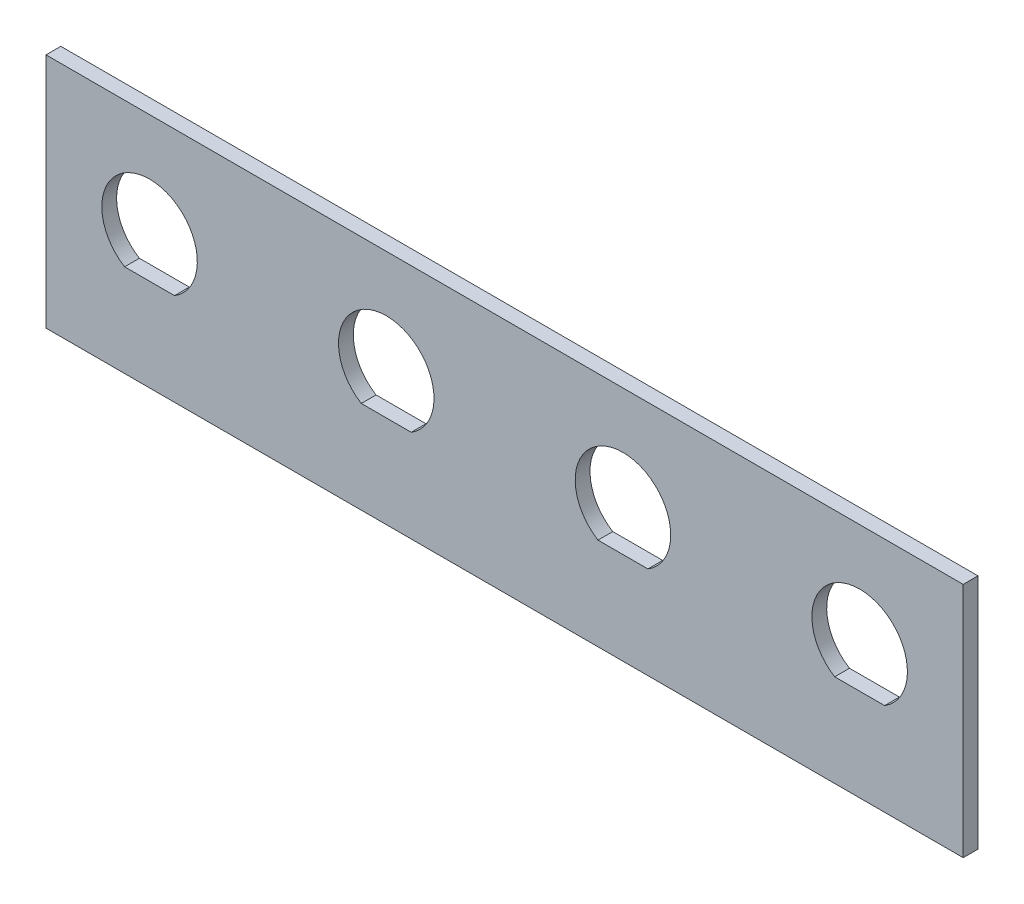
SolidWorks part; units mm, degrees
material "6061-T6 (SS)"
ref_plane "Front Plane" through (0, 0, 0) normal (0, 0, 1) x (1, 0, 0)
ref_plane "Top Plane" through (0, 0, 0) normal (0, 1, 0) x (1, 0, 0)
ref_plane "Right Plane" through (0, 0, 0) normal (1, 0, 0) x (0, 0, -1)
sketch "Sketch1" plane through (0, 0, 0) normal (0, 1, 0) x (1, 0, 0)
  line L1 (101.6, -63.5) -> (-101.6, -63.5)
  line L2 (101.6, -63.5) -> (101.6, 63.5)
  line L3 (101.6, 63.5) -> (-101.6, 63.5)
  line L4 (-101.6, -63.5) -> (-101.6, 63.5)
  line L5 (101.6, -63.5) -> (-101.6, 63.5) construction
  line L6 (101.6, 63.5) -> (-101.6, -63.5) construction
  point P0 (0, 0)
  dimension "D1" = 127
  dimension "D2" = 203.2
extrude "Boss-Extrude1" add sketch "Sketch1" along normal blind 50.8
sketch "Sketch2" plane through (0, 50.8, 0) normal (0, 1, 0) x (1, 0, 0)
  line L8 (-98.425, 60.325) -> (-98.425, -60.325)
  line L9 (98.425, 60.325) -> (-98.425, 60.325)
  line L10 (98.425, -60.325) -> (98.425, 60.325)
  line L11 (-98.425, -60.325) -> (98.425, -60.325)
  line L12 (-98.425, 60.325) -> (-98.425, -60.325)
  line L13 (98.425, 60.325) -> (-98.425, 60.325)
  line L14 (98.425, -60.325) -> (98.425, 60.325)
  line L15 (-98.425, -60.325) -> (98.425, -60.325)
  dimension "D1" = 3.175
extrude "Cut-Extrude1" cut sketch "Sketch2" against normal through all
sketch "Sketch4" plane through (0, 50.8, 0) normal (0, 1, 0) x (1, 0, 0)
  line L4 (101.6, 63.5) -> (-101.6, 63.5)
  line L5 (-101.6, 63.5) -> (-101.6, -63.5)
  line L6 (-101.6, -63.5) -> (101.6, -63.5)
  line L7 (101.6, -63.5) -> (101.6, 63.5)
  line L9 (-98.425, -60.325) -> (98.425, -60.325)
  line L10 (-98.425, -60.325) -> (-98.425, 60.325)
  line L11 (-98.425, 60.325) -> (98.425, 60.325)
  line L12 (98.425, -60.325) -> (98.425, 60.325)
  line L13 (-98.425, -60.325) -> (98.425, 60.325) construction
  line L14 (-98.425, 60.325) -> (98.425, -60.325) construction
  point P12 (0, 0)
  dimension "D1" = 3.175
  dimension "D2" = 3.175
  dimension "D3" = 3.175
  dimension "D4" = 3.175
extrude "Boss-Extrude2" add sketch "Sketch4" against normal blind 6.35
sketch "Sketch10" plane through (0, 0, 63.5) normal (0, 0, 1) x (1, 0, 0)
  line L0 (0, 28.575) -> (50.8, 28.575) construction
  line L1 (-101.6, 0) -> (101.6, 0) construction
  line L3 (-104.775, 19.8374) -> (104.775, 19.8374)
  line L6 (50.8, 28.575) -> (101.6, 28.575) construction
  line L7 (101.6, 50.8) -> (101.6, 0) construction
  line L8 (0, 28.575) -> (-50.8, 28.575) construction
  line L9 (-50.8, 28.575) -> (-101.6, 28.575) construction
  line L10 (-101.6, 50.8) -> (-101.6, 0) construction
  circle A0 centre (-76.2, 28.575) radius 10.2489
  circle A1 centre (-25.4, 28.575) radius 10.2489
  circle A2 centre (25.4, 28.575) radius 10.2489
  circle A3 centre (76.2, 28.575) radius 10.2489
  point P5 (-76.2, 28.575)
  point P9 (-25.4, 28.575)
  point P12 (25.4, 28.575)
  point P13 (76.2, 28.575)
  dimension "D2" = 28.575
  dimension "D1" = 20.4978
  dimension "D3" = 8.7376
extrude "Cut-Extrude5" cut sketch "Sketch10" against normal through all
sketch "Sketch12" plane through (101.6, 0, 0) normal (1, 0, 0) x (0, 0, -1)
  line L0 (63.5, 28.575) -> (-63.5, 28.575) construction
  line L1 (63.5, 50.8) -> (63.5, 0) construction
  line L2 (-63.5, 50.8) -> (-63.5, 0) construction
  line L4 (-63.5, 19.8374) -> (63.5, 19.8374)
  circle A0 centre (-25.4, 28.575) radius 10.2489
  circle A1 centre (25.4, 28.575) radius 10.2489
  point P6 (63.5, 28.575)
  point P7 (-25.4, 28.575)
  point P10 (25.4, 28.575)
  dimension "D2" = 8.7376
  dimension "D3" = 20.4978
  dimension "D1" = 38.1
  dimension "D4" = 38.1
extrude "Cut-Extrude6" cut sketch "Sketch12" against normal up to next
sketch "Sketch13" plane through (-101.6, 0, 0) normal (-1, 0, 0) x (0, 0, 1)
  line L0 (63.5, 25.4) -> (-63.5, 25.4) construction
  line L1 (63.5, 50.8) -> (63.5, 0) construction
  line L2 (-63.5, 50.8) -> (-63.5, 0) construction
  line L4 (-63.5, 50.8) -> (63.5, 50.8) construction
  circle A0 centre (12.7, 28.575) radius 12.554
  point P6 (25.4, 25.4)
  point P7 (12.7, 28.575)
  dimension "D3" = 25.1079
  dimension "D4" = 22.225
  dimension "D1" = 38.1
  dimension "D2" = 76.2
extrude "Cut-Extrude7" cut sketch "Sketch13" against normal up to next
sketch "Sketch14" plane through (0, 50.8, 0) normal (0, 1, 0) x (1, 0, 0)
  line L0 (-98.425, -60.325) -> (-98.425, -63.5)
  line L1 (-101.6, -63.5) -> (101.6, -63.5) construction
  line L2 (98.425, -60.325) -> (98.425, -63.5)
  line L3 (98.425, -63.5) -> (101.6, -63.5)
  line L4 (101.6, -63.5) -> (101.6, 63.5)
  line L5 (101.6, 63.5) -> (-101.6, 63.5)
  line L6 (-101.6, 63.5) -> (-101.6, -63.5)
  line L7 (-101.6, -63.5) -> (-98.425, -63.5)
  line L8 (-98.425, -60.325) -> (98.425, -60.325)
extrude "Cut-Extrude8" cut sketch "Sketch14" against normal through all
